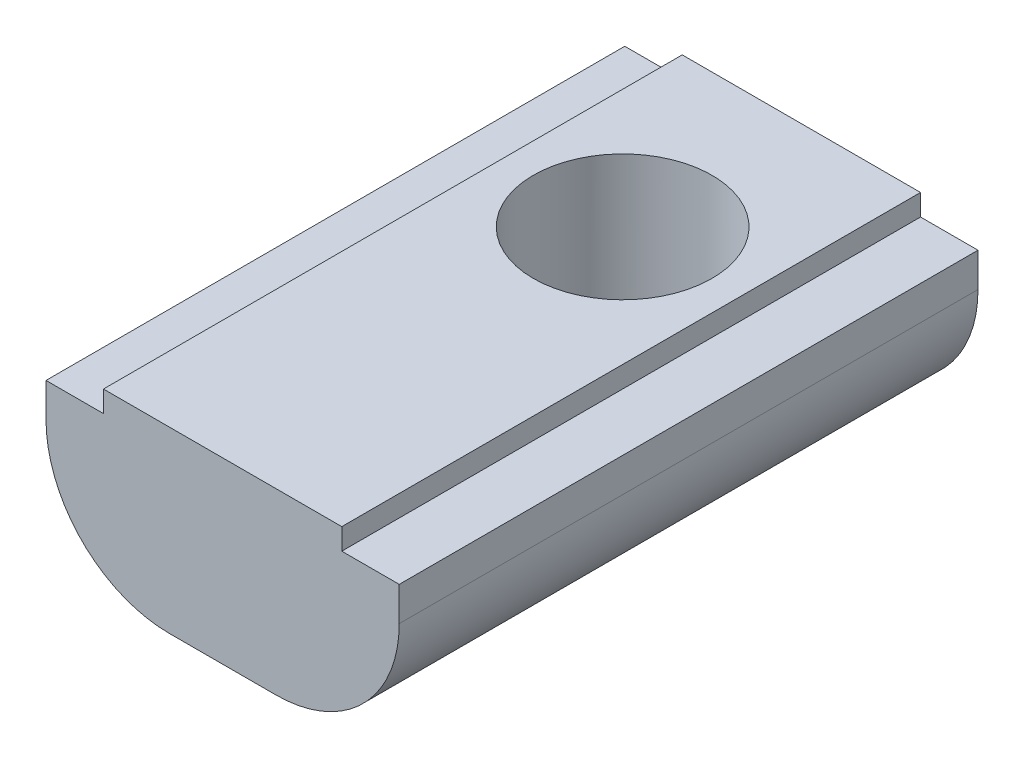
SolidWorks part; units mm, degrees
material "Plain Carbon Steel"
ref_plane "Front Plane" through (0, 0, 0) normal (0, 0, 1) x (1, 0, 0)
ref_plane "Top Plane" through (0, 0, 0) normal (0, 1, 0) x (1, 0, 0)
ref_plane "Right Plane" through (0, 0, 0) normal (1, 0, 0) x (0, 0, -1)
sketch "Sketch1" plane through (0, 0, 0) normal (0, 0, 1) x (1, 0, 0)
  line L0 (2.8, 0) -> (-2.8, 0)
  line L1 (-2.8, 0) -> (-2.8, -0.5)
  line L2 (-2.8, -0.5) -> (-4.15, -0.5)
  line L3 (-4.15, -0.5) -> (-4.15, -1.3)
  line L4 (1.25, -4.2) -> (-1.25, -4.2)
  line L5 (0, -4.2) -> (0, 0) construction
  line L6 (4.15, -0.5) -> (4.15, -1.3)
  line L7 (2.8, -0.5) -> (4.15, -0.5)
  line L8 (2.8, 0) -> (2.8, -0.5)
  arc A0 (-1.25, -4.2) -> (-4.15, -1.3) centre (-1.25, -1.3) cw
  arc A1 (1.25, -4.2) -> (4.15, -1.3) centre (1.25, -1.3) ccw
  dimension "D1" = 5.6
  dimension "D2" = 4.2
  dimension "D3" = 0.5
  dimension "D4" = 2.5
  dimension "D5" = 8.3
extrude "Boss-Extrude1" add sketch "Sketch1" along normal blind 13.6
hole_wizard "M5x0.8 Tapped Hole1" positions "Sketch3" profile "Sketch2" tap size "M5x0.8" standard "ANSI Metric" end condition through all
sketch "Sketch3" plane through (0, 0, 0) normal (0, 1, 0) x (1, 0, 0)
  line L0 (0, 0) -> (0, -4.2) construction
  point P1 (0, -4.2)
  dimension "D1" = 4.2
sketch "Sketch2" plane through (0, 0, 4.2) normal (1, 0, 0) x (0, 0, 1)
  line L0 (0, 0) -> (0, 4.2)
  line L1 (0, 4.2) -> (2.1, 4.2)
  line L2 (2.1, 4.2) -> (2.1, 0)
  line L5 (2.1, 0) -> (0, 0)
  line L11 (0, -6.35) -> (0, 107.95) construction
  dimension "Thread Major Dia." = 4.2
  dimension "Thru Tap Drill Depth" = 4.2
